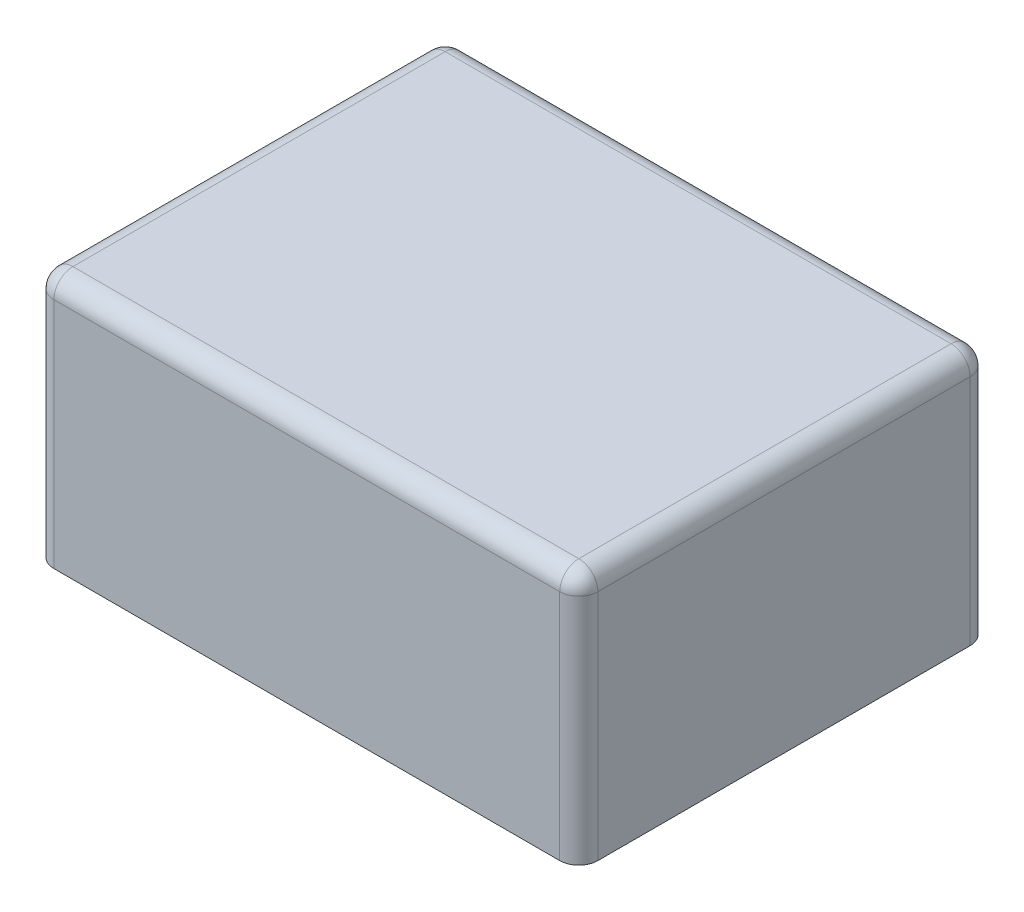
SolidWorks part; units mm, degrees
ref_plane "前视基准面" through (0, 0, 0) normal (0, 0, 1) x (1, 0, 0)
ref_plane "上视基准面" through (0, 0, 0) normal (0, 1, 0) x (1, 0, 0)
ref_plane "右视基准面" through (0, 0, 0) normal (1, 0, 0) x (0, 0, -1)
other "Configuration Table"
sketch "草图1" plane through (0, 0, 0) normal (0, 1, 0) x (1, 0, 0)
  line L1 (1, 0) -> (27.5, 0)
  line L2 (0, 1) -> (0, 20.5)
  line L3 (1, 21.5) -> (27.5, 21.5)
  line L4 (28.5, 1) -> (28.5, 20.5)
  arc A0 (1, 0) -> (0, 1) centre (1, 1) cw
  arc A1 (27.5, 0) -> (28.5, 1) centre (27.5, 1) ccw
  arc A2 (28.5, 20.5) -> (27.5, 21.5) centre (27.5, 20.5) ccw
  arc A3 (0, 20.5) -> (1, 21.5) centre (1, 20.5) cw
  point P7 (0, 0)
  point P10 (28.5, 0)
  point P13 (28.5, 21.5)
  dimension "D3" = 1
  dimension "D1" = 28.5
  dimension "D2" = 21.5
extrude "凸台-拉伸1" add sketch "草图1" along normal blind 13.2
fillet "圆角1" radius 1 8 edges at (0.2929, 13.2, -0.2929) (0.2929, 13.2, -21.2071) (28.2071, 13.2, -21.2071) (28.2071, 13.2, -0.2929) (0, 13.2, -10.75) (14.25, 13.2, -21.5) (28.5, 13.2, -10.75) (14.25, 13.2, 0)
